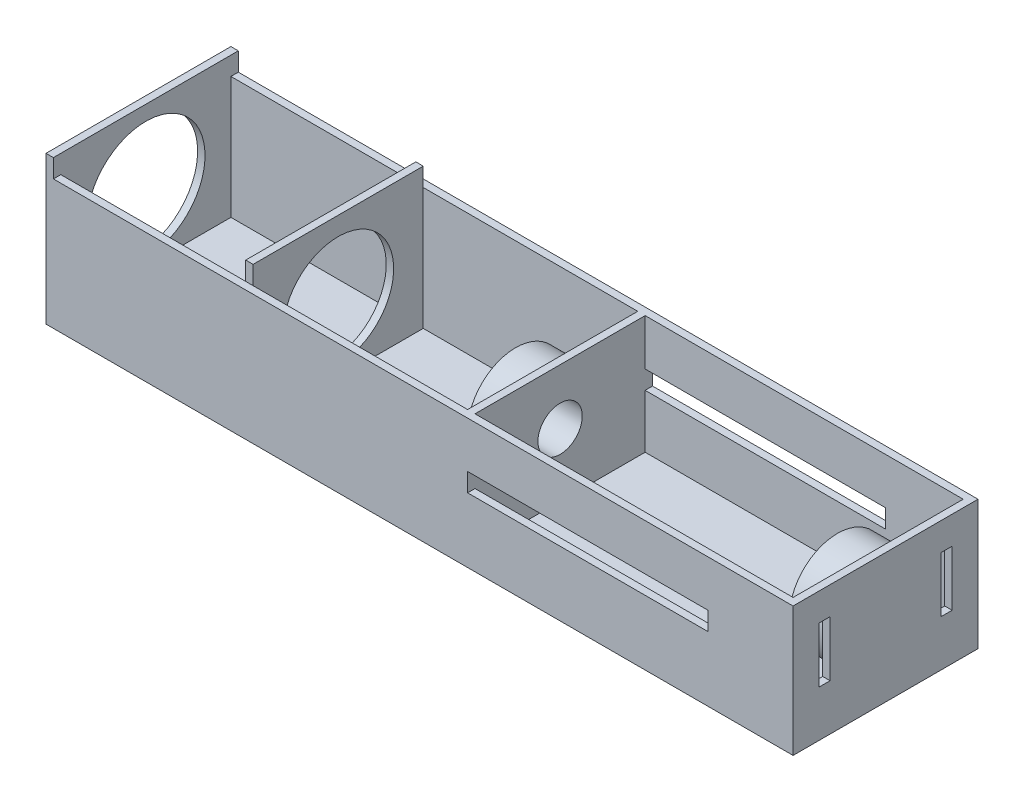
SolidWorks part; units mm, degrees
ref_plane "前基準面" through (0, 0, 0) normal (0, 0, 1) x (1, 0, 0)
ref_plane "上基準面" through (0, 0, 0) normal (0, 1, 0) x (1, 0, 0)
ref_plane "右基準面" through (0, 0, 0) normal (1, 0, 0) x (0, 0, -1)
sketch "草圖1" plane through (0, 0, 0) normal (0, 1, 0) x (1, 0, 0)
  line L1 (-45, -25) -> (45, -25)
  line L2 (-45, -25) -> (-45, 25)
  line L3 (-45, 25) -> (45, 25)
  line L4 (45, -25) -> (45, 25)
  line L5 (-45, -25) -> (45, 25) construction
  line L6 (-45, 25) -> (45, -25) construction
  point P0 (0, 0)
  dimension "D1" = 50
  dimension "D2" = 90
extrude "填料-伸長1" add sketch "草圖1" along normal blind 35
sketch "草圖2" plane through (0, 35, 0) normal (0, 1, 0) x (1, 0, 0)
  line L0 (45, 25) -> (-45, 25) construction
  line L1 (-43, -23) -> (43, -23)
  line L2 (-43, -23) -> (-43, 23)
  line L3 (-43, 23) -> (43, 23)
  line L4 (43, -23) -> (43, 23)
  line L5 (-43, -23) -> (43, 23) construction
  line L6 (-43, 23) -> (43, -23) construction
  line L7 (45, -25) -> (45, 25) construction
  point P0 (0, 0)
  dimension "D1" = 2
  dimension "D2" = 2
extrude "除料-伸長1" cut sketch "草圖2" against normal blind 32
sketch "草圖3" plane through (-45, 0, 0) normal (-1, 0, 0) x (0, 0, 1)
  line L0 (-25, 20) -> (25, 20) construction
  line L3 (-25, 0) -> (25, 0) construction
  line L4 (-25, 35) -> (25, 35) construction
  line L5 (25, 35) -> (25, 0) construction
  line L6 (-25, 35) -> (-25, 0) construction
  circle A0 centre (0, 20) radius 6
  point P2 (0, 0)
  point P8 (0, 0)
  point P10 (6.7649, 22.5)
  point P11 (0, 0)
  point P12 (6.145, 22.5)
  point P13 (10.5122, 22.5)
  point P14 (-7.6594, 22.5)
  point P15 (0, 0)
  point P18 (9.4413, 22.5)
  point P19 (0, 0)
  dimension "D1" = 12
  dimension "D2" = 15
extrude "除料-伸長2" cut sketch "草圖3" against normal up to surface (2 mm away) up to face at (-43, 19, 0)
sketch "草圖4" plane through (43, 0, 0) normal (-1, 0, 0) x (0, 0, 1)
  line L0 (-23, 20) -> (23, 20) construction
  line L1 (-23, 3) -> (-23, 35) construction
  line L2 (23, 3) -> (23, 35) construction
  line L3 (23, 35) -> (-23, 35) construction
  circle A0 centre (0, 20) radius 13
  circle A1 centre (0, 20) radius 6
  dimension "D2" = 12
  dimension "D3" = 26
  dimension "D1" = 15
extrude "填料-伸長2" add sketch "草圖4" along normal blind 11
sketch "草圖5" plane through (-43, 0, 0) normal (1, 0, 0) x (0, 0, -1)
  circle A0 centre (0, 20) radius 6
  circle A1 centre (0, 20) radius 13
  circle A2 centre (0, 20) radius 6 construction
  point P4 (0, 17.5)
  point P5 (0, 0)
  dimension "D1" = 26
extrude "填料-伸長4" add sketch "草圖5" against normal blind 12
sketch "草圖6" plane through (0, 0, -25) normal (0, 0, -1) x (-1, 0, 0)
  line L0 (-22, 20) -> (43, 20) construction
  line L1 (-22, 22.5) -> (43, 22.5)
  line L2 (-22, 22.5) -> (-22, 17.5)
  line L3 (-22, 17.5) -> (43, 17.5)
  line L4 (43, 22.5) -> (43, 17.5)
  line L5 (-45, 35) -> (45, 35) construction
  line L6 (-45, 35) -> (-45, 0) construction
  dimension "D1" = 15
  dimension "D2" = 5
  dimension "D3" = 65
  dimension "D4" = 23
extrude "除料-伸長3" cut sketch "草圖6" against normal through all
sketch "草圖7" plane through (45, 0, 0) normal (1, 0, 0) x (0, 0, -1)
  line L0 (-25, 27.5) -> (25, 27.5) construction
  line L1 (-25, 35) -> (-25, 0) construction
  line L2 (25, 35) -> (25, 0) construction
  line L3 (-25, 12.5) -> (25, 12.5) construction
  line L4 (-25, 35) -> (25, 35) construction
  line L5 (-15, 20) -> (15, 20) construction
  line L6 (-18, 27.5) -> (-15, 27.5)
  line L7 (-18, 27.5) -> (-18, 12.5)
  line L8 (-18, 12.5) -> (-15, 12.5)
  line L9 (-15, 27.5) -> (-15, 12.5)
  line L10 (15, 27.5) -> (18, 27.5)
  line L11 (15, 27.5) -> (15, 12.5)
  line L12 (15, 12.5) -> (18, 12.5)
  line L13 (18, 27.5) -> (18, 12.5)
  line L14 (0, 14) -> (0, 26) construction
  circle A0 centre (0, 20) radius 6 construction
  circle A1 centre (0, 20) radius 6 construction
  point P28 (0, 20)
  dimension "D1" = 15
  dimension "D2" = 7.5
  dimension "D3" = 3
  dimension "D4" = 3
  dimension "D5" = 30
extrude "除料-伸長4" cut sketch "草圖7" against normal blind 30
sketch "草圖8" plane through (-45, 0, 0) normal (-1, 0, 0) x (0, 0, 1)
  line L0 (-25, 0) -> (25, 0) construction
  line L1 (-25, 35) -> (-23, 35)
  line L2 (-25, 35) -> (-25, 0)
  line L3 (-25, 0) -> (-23, 0)
  line L4 (-23, 35) -> (-23, 2)
  line L5 (-25, 35) -> (25, 35) construction
  line L6 (25, 35) -> (23, 35)
  line L7 (25, 35) -> (25, 0)
  line L8 (25, 0) -> (23, 0)
  line L9 (23, 35) -> (23, 2)
  line L10 (23, 0) -> (-23, 0)
  line L11 (23, 2) -> (-23, 2)
  dimension "D1" = 2
  dimension "D2" = 2
  dimension "D3" = 2
extrude "填料-伸長5" add sketch "草圖8" along normal blind 110
sketch "草圖9" plane through (-155, 0, 0) normal (-1, 0, 0) x (0, 0, 1)
  line L1 (25, 40) -> (-25, 40)
  line L2 (25, 40) -> (25, 0)
  line L3 (25, 0) -> (-25, 0)
  line L4 (-25, 40) -> (-25, 0)
  circle A0 centre (0, 20) radius 16
  point P9 (0, 0)
  dimension "D1" = 32
  dimension "D2" = 40
extrude "填料-伸長6" add sketch "草圖9" along normal blind 2
sketch "草圖10" plane through (0, 2, 0) normal (0, 1, 0) x (1, 0, 0)
  line L0 (-155, 23) -> (-45, 23) construction
  line L1 (-105, 23) -> (-103, 23)
  line L2 (-105, 23) -> (-105, -23)
  line L3 (-105, -23) -> (-103, -23)
  line L4 (-103, 23) -> (-103, -23)
  line L5 (-155, -23) -> (-45, -23) construction
  line L6 (-155, -23) -> (-155, 23) construction
  dimension "D1" = 2
  dimension "D2" = 50
extrude "填料-伸長7" add sketch "草圖10" along normal up to surface (38 mm away) up to face at (-156, 40, 0)
sketch "草圖11" plane through (-105, 0, 0) normal (-1, 0, 0) x (0, 0, 1)
  circle A0 centre (0, 20) radius 15
  dimension "D1" = 30
extrude "除料-伸長5" cut sketch "草圖11" against normal blind 10
